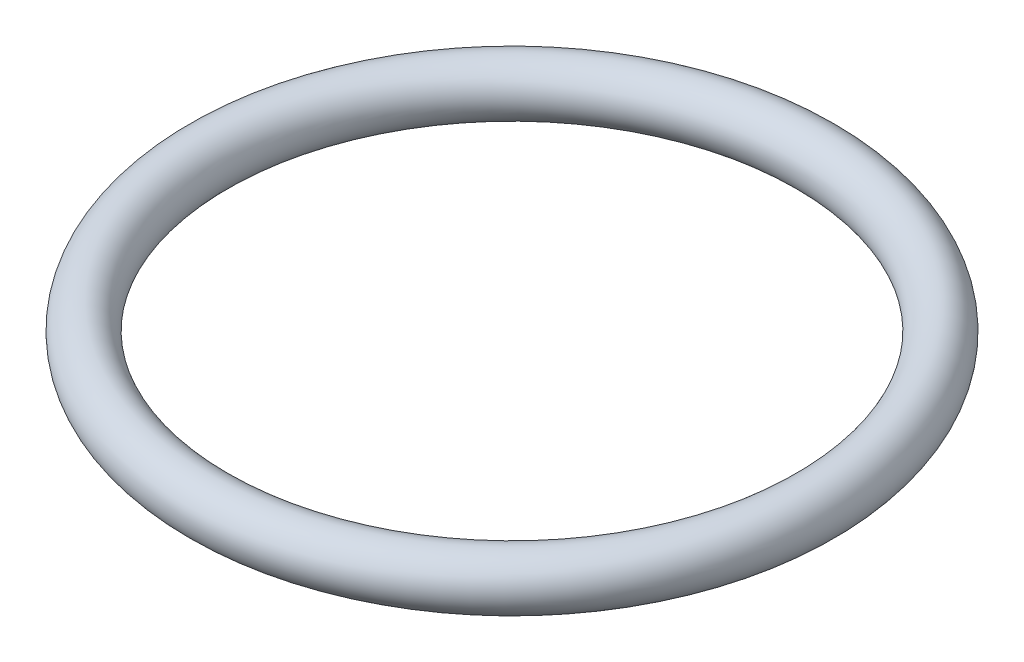
SolidWorks part; units mm, degrees
ref_plane "Front" through (0, 0, 0) normal (0, 0, 1) x (1, 0, 0)
ref_plane "Top" through (0, 0, 0) normal (0, 1, 0) x (1, 0, 0)
ref_plane "Right" through (0, 0, 0) normal (1, 0, 0) x (0, 0, -1)
sketch "Sketch2" plane through (0, 0, 0) normal (1, 0, 0) x (0, 0, -1)
  line L0 (0, 0) -> (-28.5, 0) construction
  line L1 (0, 10.5345) -> (0, -10.9644) construction
  circle A0 centre (-28.5, 0) radius 2.5
  dimension "D1" = 5
  dimension "D2" = 28.5
revolve "Revolve1" add sketch "Sketch2" angle 360 about L1
